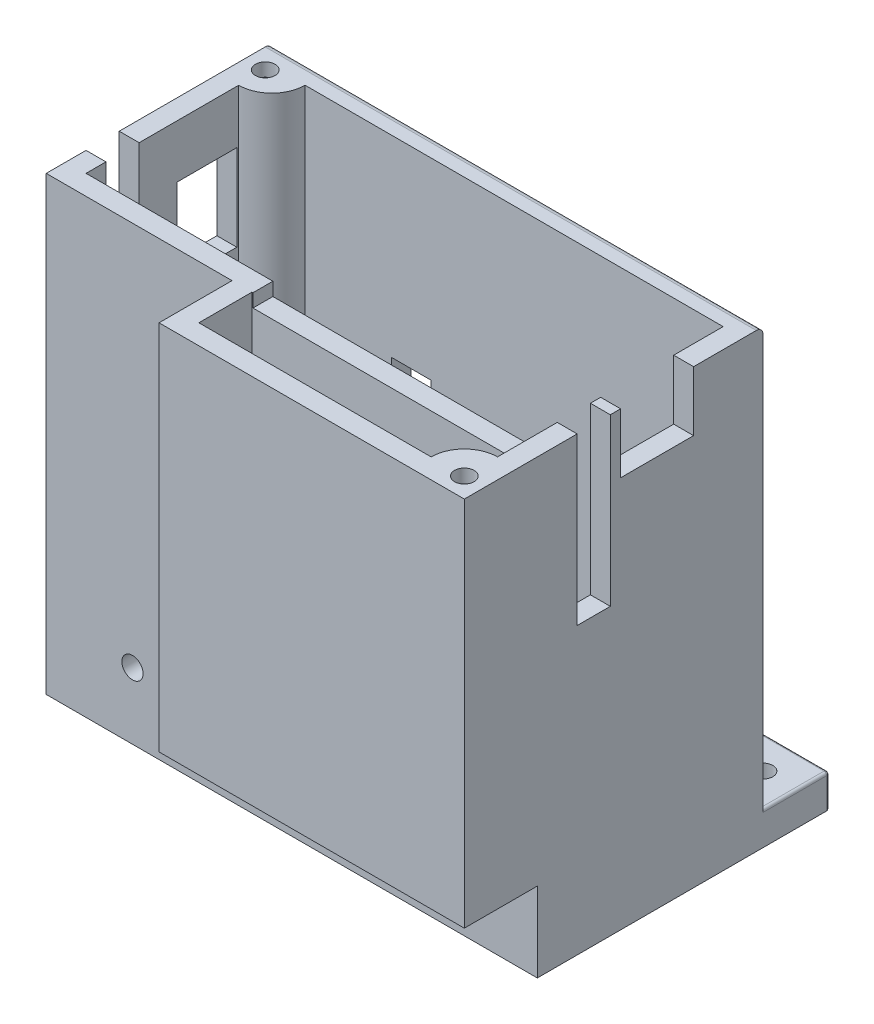
SolidWorks part; units mm, degrees
ref_plane "Front Plane" through (0, 0, 0) normal (0, 0, 1) x (1, 0, 0)
ref_plane "Top Plane" through (0, 0, 0) normal (0, 1, 0) x (1, 0, 0)
ref_plane "Right Plane" through (0, 0, 0) normal (1, 0, 0) x (0, 0, -1)
sketch "Sketch1" plane through (-3.5802, 0, -14.4177) normal (0, 1, 0) x (1, 0, 0)
  line L1 (-24.2832, 27.75) -> (49.7168, 27.75)
  line L2 (-24.2832, 27.75) -> (-24.2832, -17.25)
  line L3 (-24.2832, -17.25) -> (49.7168, -17.25)
  line L4 (49.7168, 27.75) -> (49.7168, -17.25)
  dimension "D1" = 74
  dimension "D2" = 45
extrude "Boss-Extrude1" add sketch "Sketch1" along normal blind 68
sketch "Sketch3" plane through (-3.5802, 68, -14.4177) normal (0, 1, 0) x (1, 0, 0)
  line L0 (49.7168, 27.75) -> (-24.2832, 27.75) construction
  line L1 (-21.2832, 24.75) -> (46.7168, 24.75)
  line L2 (-21.2832, 24.75) -> (-21.2832, -14.25)
  line L3 (-21.2832, -14.25) -> (46.7168, -14.25)
  line L4 (46.7168, 24.75) -> (46.7168, -14.25)
  line L5 (-24.2832, 27.75) -> (-24.2832, -17.25) construction
  line L6 (-24.2832, -17.25) -> (49.7168, -17.25) construction
  line L7 (49.7168, -17.25) -> (49.7168, 27.75) construction
  dimension "D1" = 3
  dimension "D2" = 3
  dimension "D3" = 3
  dimension "D4" = 3
extrude "Cut-Extrude2" cut sketch "Sketch3" against normal blind 65
sketch "Sketch13" plane through (-3.5802, 3, -14.4177) normal (0, 1, 0) x (1, 0, 0)
  line L0 (-21.2832, 24.75) -> (-21.2832, -14.25) construction
  line L1 (-21.2832, -3.25) -> (46.7168, -3.25)
  line L2 (-21.2832, -3.25) -> (-21.2832, -6.25)
  line L3 (-21.2832, -6.25) -> (46.7168, -6.25)
  line L4 (46.7168, -3.25) -> (46.7168, -6.25)
  line L5 (46.7168, -14.25) -> (46.7168, 24.75) construction
  line L6 (46.7168, 24.75) -> (-21.2832, 24.75) construction
  dimension "D1" = 3
  dimension "D2" = 0
  dimension "D3" = 0
  dimension "D4" = 28
extrude "Boss-Extrude3" add sketch "Sketch13" along normal blind 65
sketch "Sketch14" plane through (-27.8634, 0, -14.4177) normal (-1, 0, 0) x (0, 0, 1)
  line L0 (-27.75, 0) -> (17.25, 0) construction
  line L1 (-4.75, 10) -> (0.25, 10)
  line L2 (-4.75, 10) -> (-4.75, 68)
  line L3 (-4.75, 68) -> (0.25, 68)
  line L4 (0.25, 10) -> (0.25, 68)
  line L5 (-27.75, 68) -> (17.25, 68) construction
  line L6 (-27.75, 68) -> (-27.75, 0) construction
  dimension "D1" = 5
  dimension "D2" = 10
  dimension "D3" = 0
  dimension "D4" = 23
extrude "Cut-Extrude5" cut sketch "Sketch14" against normal blind 23
sketch "Sketch15" plane through (46.1366, 0, -14.4177) normal (1, 0, 0) x (0, 0, -1)
  line L0 (-17.25, 68) -> (27.75, 68) construction
  line L1 (4.75, 68) -> (-0.25, 68)
  line L2 (4.75, 68) -> (4.75, 43)
  line L3 (4.75, 43) -> (-0.25, 43)
  line L4 (-0.25, 68) -> (-0.25, 43)
  line L5 (-17.25, 0) -> (27.75, 0) construction
  line L6 (27.75, 68) -> (27.75, 0) construction
  line L7 (-3.25, 68) -> (-3.25, 3) construction
  point P4 (2.25, 68)
  point P9 (4.75, 55.5)
  dimension "D1" = 5
  dimension "D2" = 0
  dimension "D3" = 43
  dimension "D4" = 23
  dimension "D5" = 3
  dimension "D6" = 25
extrude "Cut-Extrude6" cut sketch "Sketch15" against normal blind 3
sketch "Sketch16" plane through (-3.5802, 3, -14.4177) normal (0, 1, 0) x (1, 0, 0)
  line L0 (-21.2832, 24.75) -> (-21.2832, -3.25) construction
  line L1 (-8.2832, 19.75) -> (6.7168, 19.75)
  line L2 (-8.2832, 19.75) -> (-8.2832, 9.75)
  line L3 (-8.2832, 9.75) -> (6.7168, 9.75)
  line L4 (6.7168, 19.75) -> (6.7168, 9.75)
  line L5 (46.7168, -3.25) -> (-21.2832, -3.25) construction
  dimension "D1" = 10
  dimension "D2" = 15
  dimension "D3" = 13
  dimension "D4" = 13
sketch "Sketch18" plane through (-3.5802, 0, -11.1677) normal (0, 0, -1) x (-1, 0, 0)
  line L0 (21.2832, 68) -> (21.2832, 3) construction
  line L1 (-46.7168, 3) -> (21.2832, 3) construction
  circle A0 centre (11.2832, 10) radius 1.6
  dimension "D1" = 10
  dimension "D2" = 7
  dimension "D3" = 7
extrude "Cut-Extrude8" cut sketch "Sketch18" against normal blind 3
sketch "Sketch20" plane through (0, 0, -42.1677) normal (0, 0, -1) x (-1, 0, 0)
  line L0 (-46.1366, 0) -> (27.8634, 0) construction
  line L1 (27.8634, 68) -> (27.8634, 0) construction
  circle A0 centre (9.8634, 8) radius 4
  dimension "D1" = 8
  dimension "D3" = 8
  dimension "D2" = 18
extrude "Cut-Extrude9" cut sketch "Sketch20" against normal blind 18
sketch "Sketch21" plane through (0, 0, 0) normal (0, -1, 0) x (1, 0, 0)
  line L0 (46.1366, 2.8323) -> (46.1366, -42.1677) construction
  line L2 (-27.8634, 2.8323) -> (46.1366, 2.8323) construction
  line L3 (46.1366, -4.1677) -> (46.1366, 2.8323)
  line L4 (46.1366, 2.8323) -> (39.1366, 2.8323)
  arc A0 (39.1366, 2.8323) -> (46.1366, -4.1677) centre (43.1366, -0.1677) ccw
  dimension "D3" = 10
  dimension "D1" = 3
  dimension "D2" = 3
extrude "Boss-Extrude4" add sketch "Sketch21" against normal blind 68
sketch "Sketch23" plane through (0, 0, 0) normal (0, -1, 0) x (1, 0, 0)
  line L0 (46.1366, 2.8323) -> (46.1366, -42.1677) construction
  line L1 (-27.8634, 2.8323) -> (46.1366, 2.8323) construction
  circle A0 centre (43.1366, -0.1677) radius 1.6
  dimension "D1" = 3
  dimension "D2" = 3
extrude "Cut-Extrude10" cut sketch "Sketch23" against normal blind 66
sketch "Sketch24" plane through (0, 0, 0) normal (0, -1, 0) x (1, 0, 0)
  line L0 (-27.8634, -42.1677) -> (-27.8634, 2.8323) construction
  line L1 (46.1366, -42.1677) -> (-27.8634, -42.1677) construction
  line L2 (-20.8634, -42.1677) -> (-27.8634, -42.1677)
  line L3 (-27.8634, -42.1677) -> (-27.8634, -35.1677)
  arc A0 (-20.8634, -42.1677) -> (-27.8634, -35.1677) centre (-24.8634, -39.1677) ccw
  dimension "D1" = 3
  dimension "D2" = 3
extrude "Boss-Extrude5" add sketch "Sketch24" against normal blind 68
sketch "Sketch25" plane through (0, 0, 0) normal (0, -1, 0) x (1, 0, 0)
  line L0 (-27.8634, -42.1677) -> (-27.8634, 2.8323) construction
  line L1 (46.1366, -42.1677) -> (-27.8634, -42.1677) construction
  circle A0 centre (-24.8634, -39.1677) radius 1.6
  dimension "D1" = 3
  dimension "D2" = 3
extrude "Cut-Extrude11" cut sketch "Sketch25" against normal blind 66
sketch "Sketch30" plane through (0, 0, -42.1677) normal (0, 0, -1) x (-1, 0, 0)
  line L0 (-46.1366, 68) -> (-46.1366, 0) construction
  line L1 (-46.1366, 5) -> (-36.1366, 5)
  line L2 (-46.1366, 5) -> (-46.1366, 0)
  line L3 (-46.1366, 0) -> (-36.1366, 0)
  line L4 (-36.1366, 5) -> (-36.1366, 0)
  line L5 (-46.1366, 0) -> (27.8634, 0) construction
  dimension "D1" = 5
  dimension "D2" = 10
  dimension "D3" = 0
  dimension "D4" = 0
fillet "Fillet2" radius 1 1 edges at (9.1366, 68, -42.1677)
extrude "Boss-Extrude6" add sketch "Sketch30" along normal blind 10
sketch "Sketch33" plane through (0, 0, 0) normal (0, -1, 0) x (1, 0, 0)
  line L0 (46.1366, -52.1677) -> (46.1366, 2.8323) construction
  line L1 (46.1366, -52.1677) -> (36.1366, -52.1677) construction
  circle A0 centre (41.1366, -47.1677) radius 1.48
  dimension "D1" = 5
  dimension "D2" = 5
extrude "Cut-Extrude13" cut sketch "Sketch33" against normal blind 5
sketch "Sketch34" plane through (0, 0, -42.1677) normal (0, 0, -1) x (-1, 0, 0)
  line L1 (17.8634, 5) -> (27.8634, 5)
  line L2 (17.8634, 5) -> (17.8634, 0)
  line L3 (17.8634, 0) -> (27.8634, 0)
  line L4 (27.8634, 5) -> (27.8634, 0)
  dimension "D1" = 5
  dimension "D2" = 10
extrude "Boss-Extrude8" add sketch "Sketch34" along normal blind 10
sketch "Sketch35" plane through (0, 0, 0) normal (0, -1, 0) x (1, 0, 0)
  line L0 (-17.8634, -52.1677) -> (-17.8634, -42.1677) construction
  line L1 (-17.8634, -52.1677) -> (-27.8634, -52.1677) construction
  circle A0 centre (-22.8634, -47.1677) radius 1.48
  dimension "D1" = 5
  dimension "D2" = 5
extrude "Cut-Extrude14" cut sketch "Sketch35" against normal blind 5
fillet "Fillet10" radius 0.4 12 edges at (46.1366, 2.5, -52.1677) (41.1366, 0, -52.1677) (36.1366, 0, -47.1677) (36.1366, 5, -47.1677) (36.1366, 2.5, -52.1677) (46.1366, 5, -47.1677) (41.1366, 5, -52.1677) (-17.8634, 0, -47.1677) (-22.8634, 0, -52.1677) (-17.8634, 2.5, -52.1677) (-17.8634, 5, -47.1677) (-22.8634, 5, -52.1677)
sketch "Sketch43" plane through (0, 0, 2.8323) normal (0, 0, 1) x (1, 0, 0)
  line L1 (-27.8634, 68) -> (0.1366, 68)
  line L2 (-27.8634, 68) -> (-27.8634, 12)
  line L4 (0.1366, 68) -> (0.1366, 12)
  line L5 (0.1366, 12) -> (46.1366, 12)
  line L6 (46.1366, 68) -> (46.1366, 0) construction
  line L7 (46.1366, 12) -> (46.1366, 0)
  line L8 (46.1366, 0) -> (-27.8634, 0)
  line L9 (-27.8634, 0) -> (-27.8634, 12)
  dimension "D1" = 28
  dimension "D2" = 12
extrude "Cut-Extrude17" cut sketch "Sketch43" against normal blind 11
sketch "Sketch45" plane through (0, 0, 2.8323) normal (0, 0, 1) x (1, 0, 0)
  line L0 (46.1366, 12) -> (0.1366, 12) construction
  line L1 (0.1366, 68) -> (3.1366, 68)
  line L2 (0.1366, 68) -> (0.1366, 12)
  line L3 (0.1366, 12) -> (3.1366, 12)
  line L4 (3.1366, 68) -> (3.1366, 12)
  dimension "D1" = 3
extrude "Boss-Extrude9" add sketch "Sketch45" against normal blind 11
sketch "Sketch47" plane through (0, 0, 2.8323) normal (0, 0, 1) x (1, 0, 0)
  line L0 (46.1366, 68) -> (46.1366, 12) construction
  line L1 (0.1366, 12) -> (46.1366, 12)
  line L2 (0.1366, 12) -> (0.1366, 15)
  line L3 (0.1366, 15) -> (46.1366, 15)
  line L4 (46.1366, 12) -> (46.1366, 15)
  dimension "D1" = 3
extrude "Boss-Extrude10" add sketch "Sketch47" against normal blind 11
sketch "Sketch49" plane through (0, 68, 0) normal (0, 1, 0) x (1, 0, 0)
  line L0 (46.1366, -2.8323) -> (46.1366, 14.1677) construction
  line L1 (0.1366, -2.8323) -> (46.1366, -2.8323) construction
  circle A0 centre (43.1366, 0.1677) radius 1.48
  dimension "D1" = 3
  dimension "D2" = 3
extrude "Cut-Extrude18" cut sketch "Sketch49" against normal blind 56
sketch "Sketch50" plane through (0, 68, 0) normal (0, 1, 0) x (1, 0, 0)
  line L0 (-27.8634, 41.1677) -> (-27.8634, 19.1677) construction
  line L1 (46.1366, 41.1677) -> (-27.8634, 41.1677) construction
  circle A0 centre (-24.8634, 38.1677) radius 1.48
  dimension "D1" = 3
  dimension "D2" = 3
extrude "Cut-Extrude19" cut sketch "Sketch50" against normal blind 68
sketch "Sketch52" plane through (0, 0, -11.1677) normal (0, 0, -1) x (-1, 0, 0)
  line L1 (-43.1366, 68) -> (-3.2874, 68)
  line L2 (-43.1366, 68) -> (-43.1366, 66)
  line L3 (-43.1366, 66) -> (-3.2874, 66)
  line L4 (-3.2874, 68) -> (-3.2874, 66)
  dimension "D1" = 2
extrude "Cut-Extrude20" cut sketch "Sketch52" against normal blind 3
sketch "Sketch54" plane through (46.1366, 0, 0) normal (1, 0, 0) x (0, 0, -1)
  line L0 (19.1677, 68) -> (41.1677, 68) construction
  line L1 (20.7155, 68) -> (31.7155, 68)
  line L2 (20.7155, 68) -> (20.7155, 59)
  line L3 (20.7155, 59) -> (31.7155, 59)
  line L4 (31.7155, 68) -> (31.7155, 59)
  dimension "D1" = 11
  dimension "D2" = 9
extrude "Cut-Extrude21" cut sketch "Sketch54" against normal blind 3
sketch "Sketch56" plane through (-27.8634, 0, 0) normal (-1, 0, 0) x (0, 0, 1)
  line L0 (-41.1677, 68) -> (-19.1677, 68) construction
  line L1 (-33.8873, 60) -> (-24.8873, 60)
  line L2 (-33.8873, 60) -> (-33.8873, 47)
  line L3 (-33.8873, 47) -> (-24.8873, 47)
  line L4 (-24.8873, 60) -> (-24.8873, 47)
  point P6 (-30.1677, 68)
  dimension "D1" = 13
  dimension "D2" = 9
  dimension "D3" = 8
extrude "Cut-Extrude22" cut sketch "Sketch56" against normal blind 3
sketch "Sketch57" plane through (0, 0, -42.1677) normal (0, 0, -1) x (-1, 0, 0)
  line L0 (27.8634, 67) -> (-46.1366, 67) construction
  line L1 (6.8634, 33) -> (0.8634, 33)
  line L2 (6.8634, 33) -> (6.8634, 39)
  line L3 (6.8634, 39) -> (0.8634, 39)
  line L4 (0.8634, 33) -> (0.8634, 39)
  line L5 (27.8634, 67) -> (27.8634, 5) construction
  point P4 (3.8634, 39)
  dimension "D1" = 6
  dimension "D2" = 6
  dimension "D3" = 28
  dimension "D4" = 21
extrude "Cut-Extrude23" cut sketch "Sketch57" against normal blind 3
